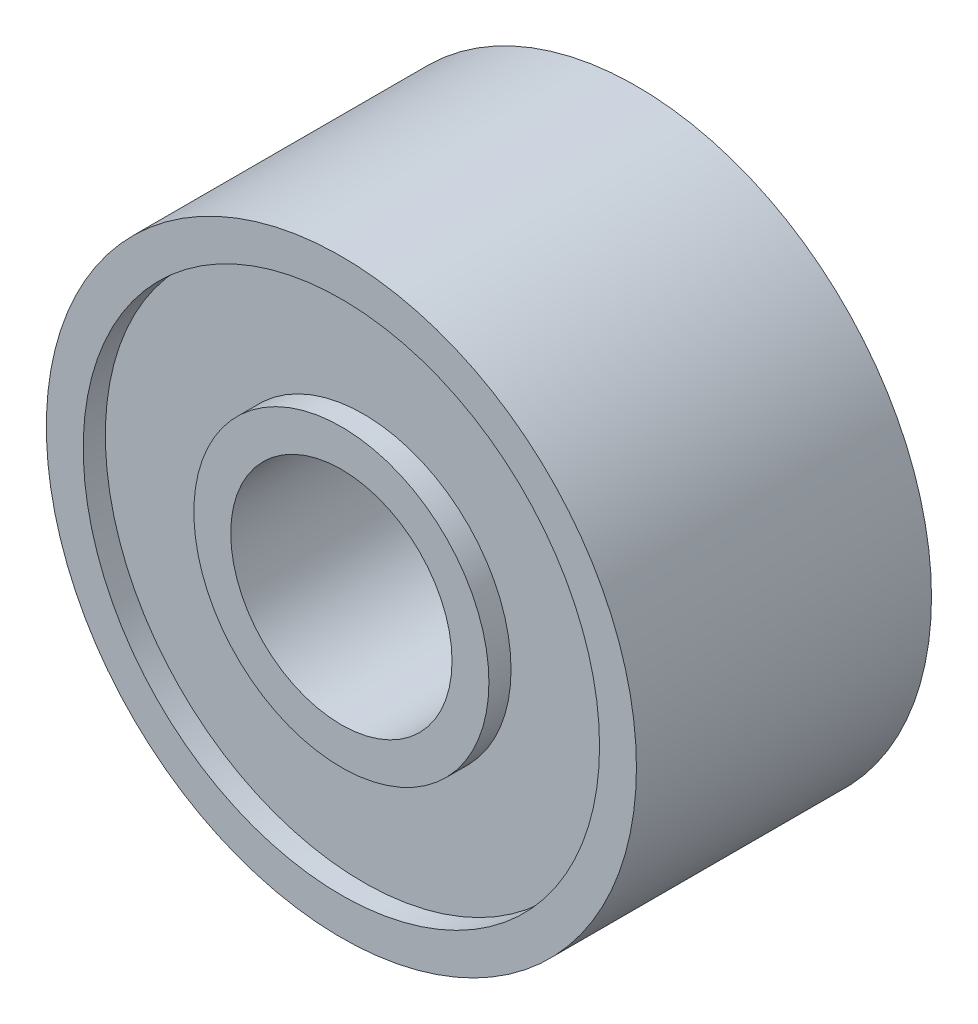
SolidWorks part; units mm, degrees
material "鉻不鏽鋼"
ref_plane "前基準面" through (0, 0, 0) normal (0, 0, 1) x (1, 0, 0)
ref_plane "上基準面" through (0, 0, 0) normal (0, 1, 0) x (1, 0, 0)
ref_plane "右基準面" through (0, 0, 0) normal (1, 0, 0) x (0, 0, -1)
sketch "草圖1" plane through (0, 0, 0) normal (0, 0, 1) x (1, 0, 0)
  circle A0 centre (0, 0) radius 4
  dimension "D1" = 8
extrude "填料-伸長1" add sketch "草圖1" along normal blind 4
sketch "草圖2" plane through (0, 0, 4) normal (0, 0, 1) x (1, 0, 0)
  circle A0 centre (0, 0) radius 1.5
  dimension "D1" = 3
extrude "除料-伸長1" cut sketch "草圖2" against normal through all
sketch "草圖3" plane through (0, 0, 4) normal (0, 0, 1) x (1, 0, 0)
  circle A0 centre (0, 0) radius 2
  circle A1 centre (0, 0) radius 3.5
  dimension "D1" = 4
  dimension "D2" = 7
extrude "除料-伸長2" cut sketch "草圖3" against normal blind 0.3
sketch "草圖4" plane through (0, 0, 0) normal (0, 0, -1) x (-1, 0, 0)
  circle A0 centre (0, 0) radius 2
  circle A1 centre (0, 0) radius 3.5
  dimension "D1" = 7
  dimension "D2" = 4
extrude "除料-伸長3" cut sketch "草圖4" against normal blind 0.3
